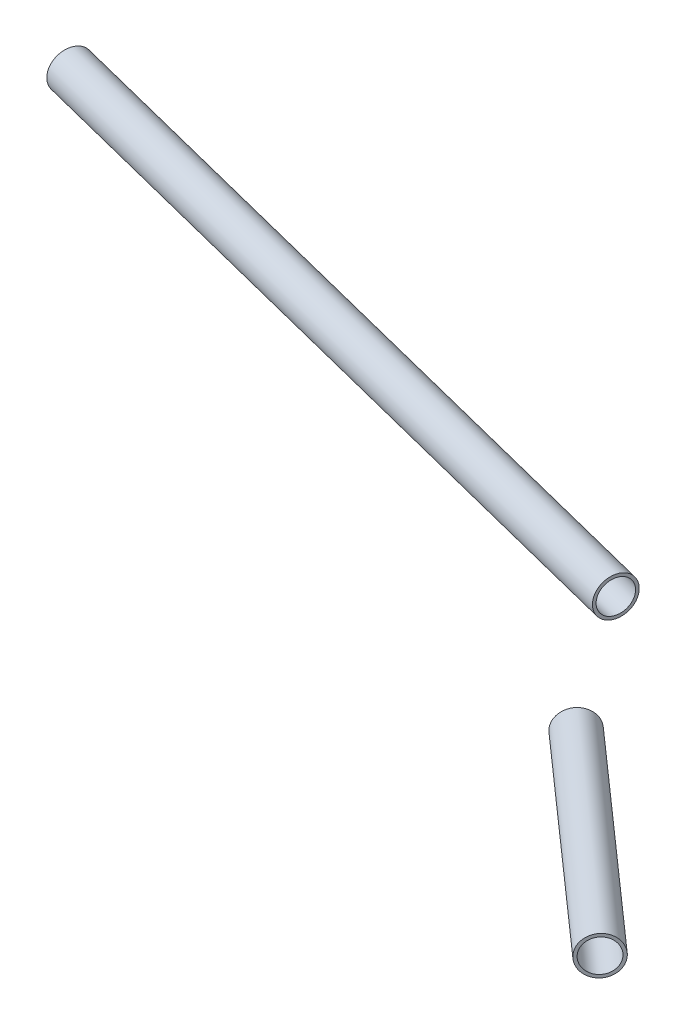
SolidWorks part; units mm, degrees
material "Thornel Mat VMA"
ref_plane "Płaszczyzna XY" through (0, 0, 0) normal (0, 0, 1) x (1, 0, 0)
ref_plane "Płaszczyzna XZ" through (0, 0, 0) normal (0, 1, 0) x (1, 0, 0)
ref_plane "Płaszczyzna YZ" through (0, 0, 0) normal (1, 0, 0) x (0, 0, -1)
sketch "Szkic1" plane through (100.1198, 0, 88.5696) normal (-0.749, 0, -0.6626) x (-0.6626, 0, 0.749)
  circle A1 centre (423.2482, 468) radius 6.35
  circle A2 centre (423.2482, 468) radius 6.35
  dimension "D1" = 0
extrude "Dodanie-wyciągnięcie1" add sketch "Szkic1" along normal up to surface (91.1644 mm away)
sketch "Szkic2" plane through (-192.2444, 0, -48.3605) normal (-0.9698, 0, -0.244) x (-0.244, 0, 0.9698)
  circle A1 centre (359.8985, 468) radius 6.35
  circle A2 centre (359.8985, 468) radius 6.35
  dimension "D1" = 0
extrude "Dodanie-wyciągnięcie2" add sketch "Szkic2" along normal up to surface (247.2288 mm away) separate body
shell "Skorupa1" thickness 1
shell "Skorupa2" thickness 1
